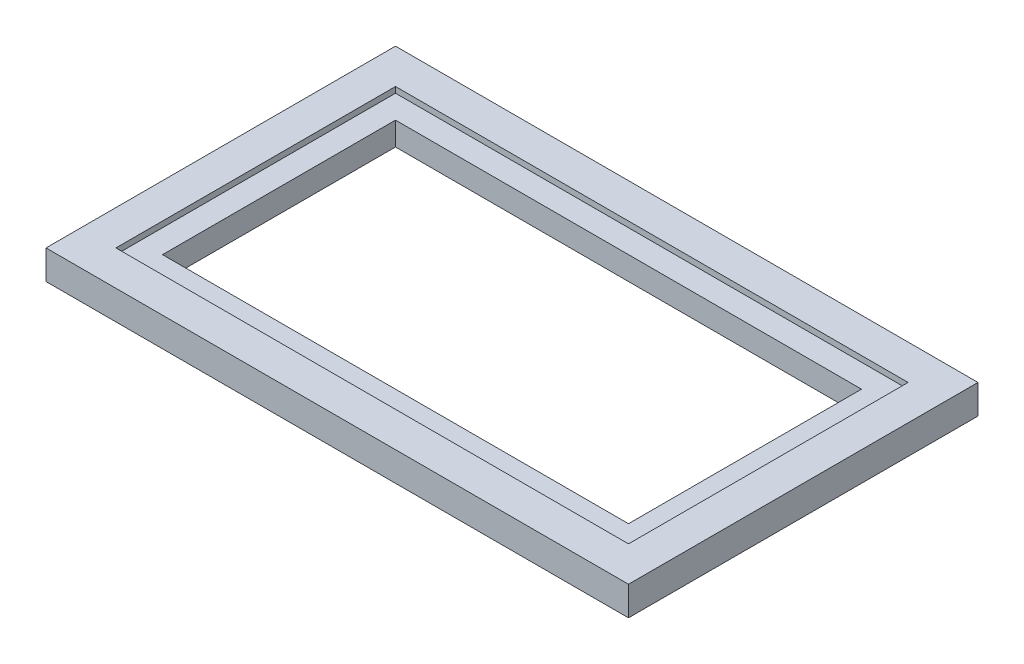
SolidWorks part; units mm, degrees
material "Ceramic Porcelain"
ref_plane "Front Plane" through (0, 0, 0) normal (0, 0, 1) x (1, 0, 0)
ref_plane "Top Plane" through (0, 0, 0) normal (0, 1, 0) x (1, 0, 0)
ref_plane "Right Plane" through (0, 0, 0) normal (1, 0, 0) x (0, 0, -1)
sketch "Sketch1" plane through (0, 0, 0) normal (0, 1, 0) x (1, 0, 0)
  line L1 (500, 300) -> (-500, 300)
  line L2 (500, 300) -> (500, -300)
  line L3 (500, -300) -> (-500, -300)
  line L4 (-500, 300) -> (-500, -300)
  line L5 (500, 300) -> (-500, -300) construction
  line L6 (500, -300) -> (-500, 300) construction
  point P0 (0, 0)
  dimension "D1" = 1000
  dimension "D2" = 600
extrude "Boss-Extrude1" add sketch "Sketch1" along normal blind 50
sketch "Sketch2" plane through (0, 50, 0) normal (0, 1, 0) x (1, 0, 0)
  line L9 (-400, 200) -> (-400, -200)
  line L10 (-400, -200) -> (400, -200)
  line L11 (400, -200) -> (400, 200)
  line L12 (400, 200) -> (-400, 200)
  line L13 (-400, 200) -> (-400, -200)
  line L14 (-400, -200) -> (400, -200)
  line L15 (400, -200) -> (400, 200)
  line L16 (400, 200) -> (-400, 200)
  dimension "D1" = 100
extrude "Cut-Extrude1" cut sketch "Sketch2" against normal through all
sketch "Sketch3" plane through (0, 50, 0) normal (0, 1, 0) x (1, 0, 0)
  line L8 (-440, 240) -> (-440, -240)
  line L9 (440, 240) -> (-440, 240)
  line L10 (440, -240) -> (440, 240)
  line L11 (-440, -240) -> (440, -240)
  line L12 (-440, 240) -> (-440, -240)
  line L13 (440, 240) -> (-440, 240)
  line L14 (440, -240) -> (440, 240)
  line L15 (-440, -240) -> (440, -240)
  dimension "D1" = 40
extrude "Cut-Extrude2" cut sketch "Sketch3" against normal blind 10
